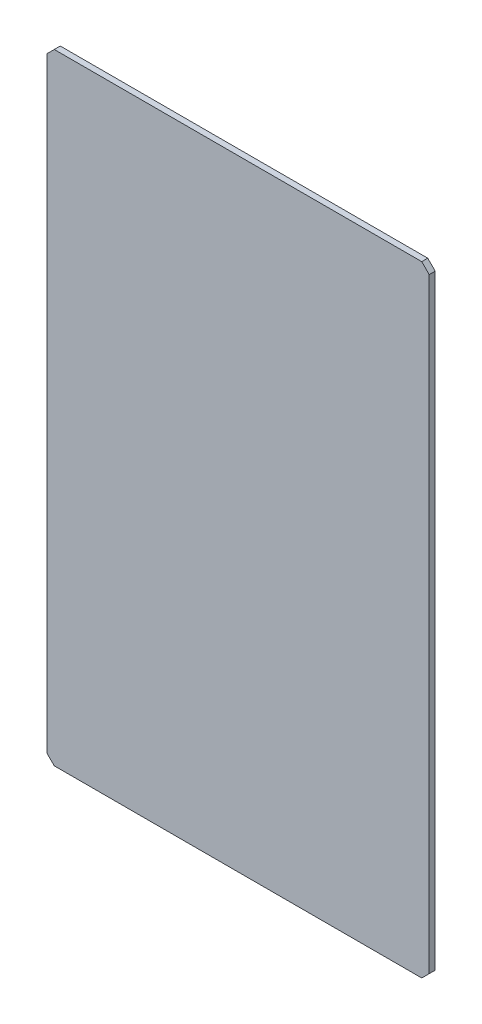
SolidWorks part; units mm, degrees
ref_plane "前视基准面" through (0, 0, 0) normal (0, 0, 1) x (1, 0, 0)
ref_plane "上视基准面" through (0, 0, 0) normal (0, 1, 0) x (1, 0, 0)
ref_plane "右视基准面" through (0, 0, 0) normal (1, 0, 0) x (0, 0, -1)
sketch "草图1" plane through (0, 0, 0) normal (0, 0, 1) x (1, 0, 0)
  line L2 (-28.2996, 98.6731) -> (-28.2996, -25.4144)
  line L3 (-28.2996, -25.4144) -> (48.2004, -25.4144)
  line L4 (48.2004, 98.6731) -> (48.2004, -25.4144)
  line L5 (-28.2996, 98.6731) -> (48.2004, 98.6731)
  line L7 (-26.2996, 99.1731) -> (46.2004, 99.1731) construction
  point P1 (0, 0)
  point P6 (0, 0)
  dimension "D1" = 76.5
  dimension "D2" = 0.5
extrude "凸台-拉伸1" add sketch "草图1" along normal blind 1.2
chamfer "倒角1" distance 1.5 angle 45 4 edges at (-28.2996, -25.4144, 0.6) (48.2004, -25.4144, 0.6) (48.2004, 98.6731, 0.6) (-28.2996, 98.6731, 0.6)
